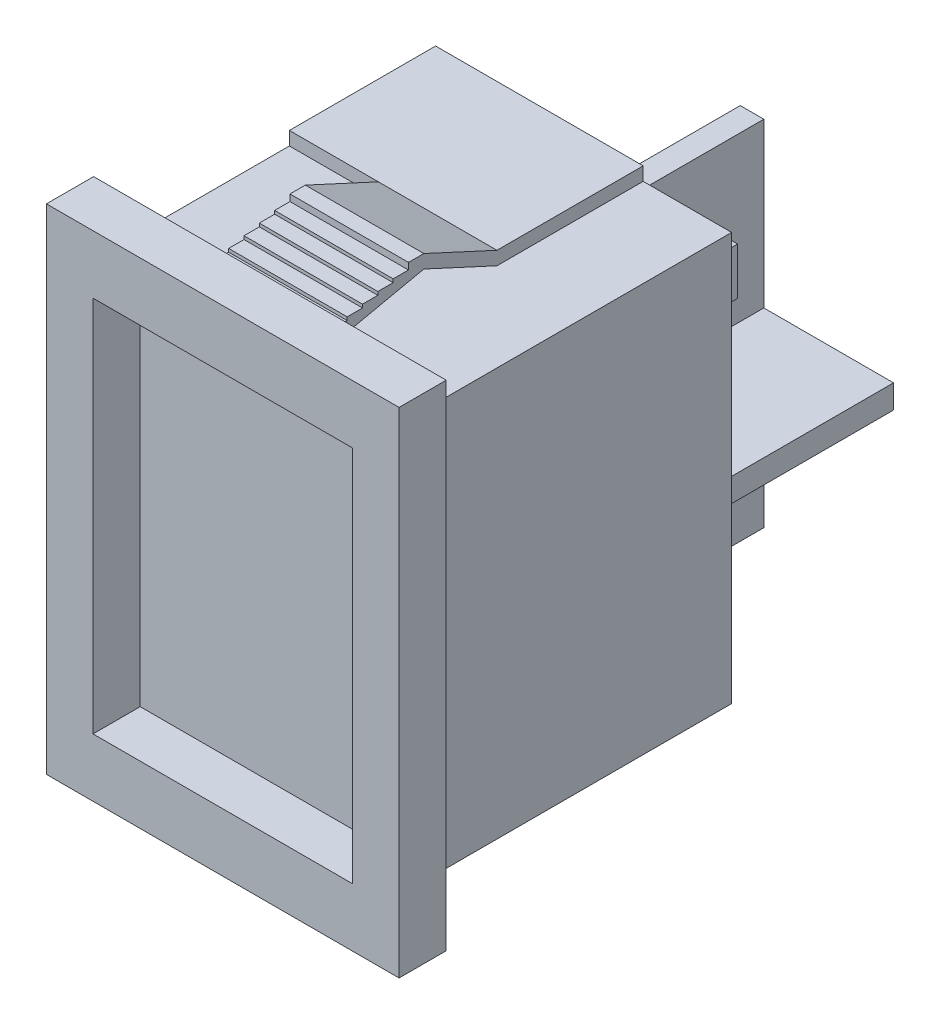
SolidWorks part; units mm, degrees
ref_plane "Front Plane" through (0, 0, 0) normal (0, 0, 1) x (1, 0, 0)
ref_plane "Top Plane" through (0, 0, 0) normal (0, 1, 0) x (1, 0, 0)
ref_plane "Right Plane" through (0, 0, 0) normal (1, 0, 0) x (0, 0, -1)
sketch "Sketch1" plane through (0, 0, 0) normal (0, 0, 1) x (1, 0, 0)
  line L1 (-7.475, 10.475) -> (7.475, 10.475)
  line L2 (-7.475, 10.475) -> (-7.475, -10.475)
  line L3 (-7.475, -10.475) -> (7.475, -10.475)
  line L4 (7.475, 10.475) -> (7.475, -10.475)
  line L5 (-5.5, 8) -> (5.5, 8)
  line L6 (-5.5, 8) -> (-5.5, -8)
  line L7 (-5.5, -8) -> (5.5, -8)
  line L8 (5.5, 8) -> (5.5, -8)
  dimension "D1" = 14.95
  dimension "D2" = 20.95
  dimension "D3" = 11
  dimension "D4" = 16
  dimension "D5" = 10.475
  dimension "D6" = 7.475
  dimension "D7" = 1.975
  dimension "D8" = 2.475
extrude "Boss-Extrude1" add sketch "Sketch1" along normal blind 2
sketch "Sketch2" plane through (0, 0, 0) normal (0, 0, -1) x (-1, 0, 0)
  line L1 (-6.275, 8.65) -> (6.275, 8.65)
  line L2 (-6.275, 8.65) -> (-6.275, -8.65)
  line L3 (-6.275, -8.65) -> (6.275, -8.65)
  line L4 (6.275, 8.65) -> (6.275, -8.65)
  dimension "D1" = 12.55
  dimension "D2" = 17.3
  dimension "D3" = 8.65
  dimension "D4" = 6.275
extrude "Boss-Extrude2" add sketch "Sketch2" along normal blind 13.3
sketch "Sketch3" plane through (-6.275, 0, 0) normal (-1, 0, 0) x (0, 0, 1)
  line L1 (-7.1, 9.22) -> (-13.3, 9.22)
  line L2 (-7.1, 9.22) -> (-7.1, -9.22)
  line L3 (-7.1, -9.22) -> (-13.3, -9.22)
  line L5 (-13.3, 9.22) -> (-13.3, -9.22)
  line L6 (-13.3, 8.65) -> (0, 8.65) construction
  line L7 (0, -8.65) -> (0, 8.65) construction
  line L9 (0, -8.65) -> (0, 8.65)
  line L10 (0, 8.65) -> (-13.3, 8.65)
  line L11 (-13.3, 8.65) -> (-13.3, -8.65)
  line L12 (-13.3, -8.65) -> (0, -8.65)
  line L15 (-13.3, 8.65) -> (-13.3, -8.65) construction
  dimension "D1" = 18.44
  dimension "D3" = 17.3
  dimension "D4" = 0.57
  dimension "D5" = 6.2
  dimension "D6" = 7.1
extrude "Boss-Extrude3" add sketch "Sketch3" against normal blind 8.8
ref_plane "Plane1" through (0, 0, 0) normal (1, 0, 0) x (0, 0, -1)
sketch "Sketch4" plane through (0, 0, 0) normal (1, 0, 0) x (0, 0, -1)
  line L0 (-4.4348, -10.65) -> (15.1231, -10.65) construction
  line L4 (4.9684, -10.65) -> (4.9684, 10.65) construction
  line L5 (-4.4348, 10.65) -> (15.1231, 10.65) construction
  line L6 (4, -13.528) -> (4, 14.734) construction
  line L7 (-5.6758, 0) -> (15.9446, 0) construction
  line L8 (7.1, -9.22) -> (4, -10.65)
  line L9 (7.1, -8.65) -> (4, -10.08)
  line L10 (0, -9.22) -> (4, -10.08)
  line L11 (0, -10.475) -> (0, 10.475) construction
  line L14 (4, -10.65) -> (3.35, -10.65)
  line L15 (2.7, -10.3705) -> (3.35, -10.3705)
  line L16 (3.35, -10.3705) -> (3.35, -10.65)
  line L17 (2.05, -10.2308) -> (2.7, -10.2308)
  line L18 (2.7, -10.2308) -> (2.7, -10.3705)
  line L19 (1.4, -10.091) -> (2.05, -10.091)
  line L20 (2.05, -10.091) -> (2.05, -10.2308)
  line L21 (0.75, -9.9513) -> (1.4, -9.9513)
  line L22 (1.4, -9.9513) -> (1.4, -10.091)
  line L23 (0.75, -9.9513) -> (0.75, -9.8115)
  line L24 (0.75, -9.8115) -> (0, -9.8115)
  line L25 (7.1, -9.22) -> (7.1, -8.65)
  line L26 (0, -9.8115) -> (0, -9.22)
  line L27 (7.1, 9.22) -> (7.1, 8.65)
  line L28 (0.75, 9.8115) -> (0, 9.8115)
  line L29 (0.75, 9.9513) -> (0.75, 9.8115)
  line L30 (1.4, 9.9513) -> (1.4, 10.091)
  line L31 (0.75, 9.9513) -> (1.4, 9.9513)
  line L32 (2.05, 10.091) -> (2.05, 10.2308)
  line L33 (1.4, 10.091) -> (2.05, 10.091)
  line L34 (2.7, 10.2308) -> (2.7, 10.3705)
  line L35 (2.05, 10.2308) -> (2.7, 10.2308)
  line L36 (3.35, 10.3705) -> (3.35, 10.65)
  line L37 (2.7, 10.3705) -> (3.35, 10.3705)
  line L38 (4, 10.65) -> (3.35, 10.65)
  line L39 (0, 9.22) -> (4, 10.08)
  line L40 (7.1, 8.65) -> (4, 10.08)
  line L41 (7.1, 9.22) -> (4, 10.65)
  line L42 (0, 9.8115) -> (0, 9.22)
  point P0 (4.9684, 0)
  dimension "D1" = 21.3
  dimension "D3" = 0.57
  dimension "D9" = 0.1397
  dimension "D10" = 0.1397
  dimension "D11" = 0.75
  dimension "D14" = 15.1231
  dimension "D15" = 15.1231
  dimension "D16" = 4.4348
  dimension "D17" = 4.4348
  dimension "D12" = 4.9684
  dimension "D13" = 9.22
  dimension "D18" = 10.2308
  dimension "D19" = 10.3705
  dimension "D2" = 1.4
  dimension "D4" = 2.05
  dimension "D5" = 2.7
  dimension "D6" = 3.35
  dimension "D7" = 4
  dimension "D8" = 9.8115
extrude "Boss-Extrude4" add sketch "Sketch4" along normal up to surface (2.525 mm away) and the other way blind 2.5 up to face at (2.525, -8.935, -10.2)
sketch "Sketch5" plane through (0, 0, -13.3) normal (0, 0, -1) x (-1, 0, 0)
  line L0 (-6.275, -8.65) -> (-2.525, -8.65) construction
  line L1 (0.5, 6.35) -> (-0.5, 6.35)
  line L2 (0.5, 6.35) -> (0.5, -0.58)
  line L3 (0.5, -8.65) -> (-0.5, -8.65)
  line L4 (-0.5, 6.35) -> (-0.5, -0.58)
  line L5 (0, 8.415) -> (0, -8.415) construction
  line L6 (-2.525, 9.22) -> (6.275, 9.22) construction
  line L7 (-6, -0.58) -> (-0.5, -0.58)
  line L8 (-6, -0.58) -> (-6, -1.58)
  line L9 (-6, -1.58) -> (-0.5, -1.58)
  line L10 (6, -0.58) -> (6, -1.58)
  line L11 (-0.5, -1.58) -> (-0.5, -8.65)
  line L12 (0.5, -0.58) -> (6, -0.58)
  line L13 (0.5, -1.58) -> (0.5, -8.65)
  line L14 (0.5, -1.58) -> (6, -1.58)
  dimension "D1" = 1
  dimension "D2" = 15
  dimension "D3" = 0.5
  dimension "D4" = 1
  dimension "D5" = 12
  dimension "D6" = 6
  dimension "D7" = 10.8
extrude "Boss-Extrude5" add sketch "Sketch5" along normal blind 7.14
sketch "Sketch6" plane through (0, 0, -13.3) normal (0, 0, -1) x (-1, 0, 0)
  line L0 (0.5, -1.58) -> (6, -1.58) construction
  line L1 (0.9829, -1.58) -> (3.4829, -1.58)
  line L2 (0.9829, -1.58) -> (0.9829, -3.58)
  line L3 (0.9829, -8.58) -> (3.4829, -8.58)
  line L4 (3.4829, -1.58) -> (3.4829, -3.58)
  line L5 (0.9829, -6.58) -> (0.9829, -8.58)
  line L6 (0.9829, -3.58) -> (3.4829, -3.58)
  line L8 (0.9829, -6.58) -> (3.4829, -6.58)
  line L10 (3.4829, -6.58) -> (3.4829, -8.58)
  line L11 (0, 12.2791) -> (0, -12.2791) construction
  line L12 (0, 12.342) -> (0, -12.342) construction
  line L13 (-3.4829, -6.58) -> (-3.4829, -8.58)
  line L14 (-0.9829, -8.58) -> (-3.4829, -8.58)
  line L15 (-0.9829, -6.58) -> (-0.9829, -8.58)
  line L16 (-0.9829, -6.58) -> (-3.4829, -6.58)
  line L17 (-3.4829, -1.58) -> (-3.4829, -3.58)
  line L18 (-0.9829, -1.58) -> (-3.4829, -1.58)
  line L19 (-0.9829, -1.58) -> (-0.9829, -3.58)
  line L20 (-0.9829, -3.58) -> (-3.4829, -3.58)
  line L21 (0.5, 6.35) -> (-0.5, 6.35) construction
  line L22 (3.025, 7.35) -> (5.525, 7.35)
  line L23 (3.025, 7.35) -> (3.025, 5.35)
  line L24 (3.025, 5.35) -> (5.525, 5.35)
  line L25 (5.525, 7.35) -> (5.525, 5.35)
  line L30 (6.275, -8.65) -> (6.275, 8.65) construction
  line L31 (-3.025, 5.35) -> (-5.525, 5.35)
  line L32 (-5.525, 7.35) -> (-5.525, 5.35)
  line L33 (-3.025, 7.35) -> (-5.525, 7.35)
  line L34 (-3.025, 7.35) -> (-3.025, 5.35)
  dimension "D1" = 7
  dimension "D2" = 2.5
  dimension "D3" = 3
  dimension "D4" = 2
  dimension "D5" = 2
  dimension "D6" = 2.5
  dimension "D7" = 1
  dimension "D8" = 0.75
extrude "Boss-Extrude6" add sketch "Sketch6" along normal blind 1
equation "\"D5@Sketch1\"=\"D2@Sketch1\"/2"
equation "\"D6@Sketch1\"=\"D1@Sketch1\"/2"
equation "\"D7@Sketch1\"=(\"D1@Sketch1\"-\"D3@Sketch1\")/2"
equation "\"D8@Sketch1\"=(\"D2@Sketch1\"-\"D4@Sketch1\")/2"
equation "\"D3@Sketch2\"=\"D2@Sketch2\"/2"
equation "\"D4@Sketch2\"=\"D1@Sketch2\"/2"
equation "\"D4@Sketch3\"=(\"D1@Sketch3\"-\"D3@Sketch3\")/2"
equation "\"D10@Sketch4\"=\"D9@Sketch4\""
equation "\"D3@Sketch5\"=\"D1@Sketch5\"/2"
equation "\"D6@Sketch5\"=\"D5@Sketch5\"/2"
